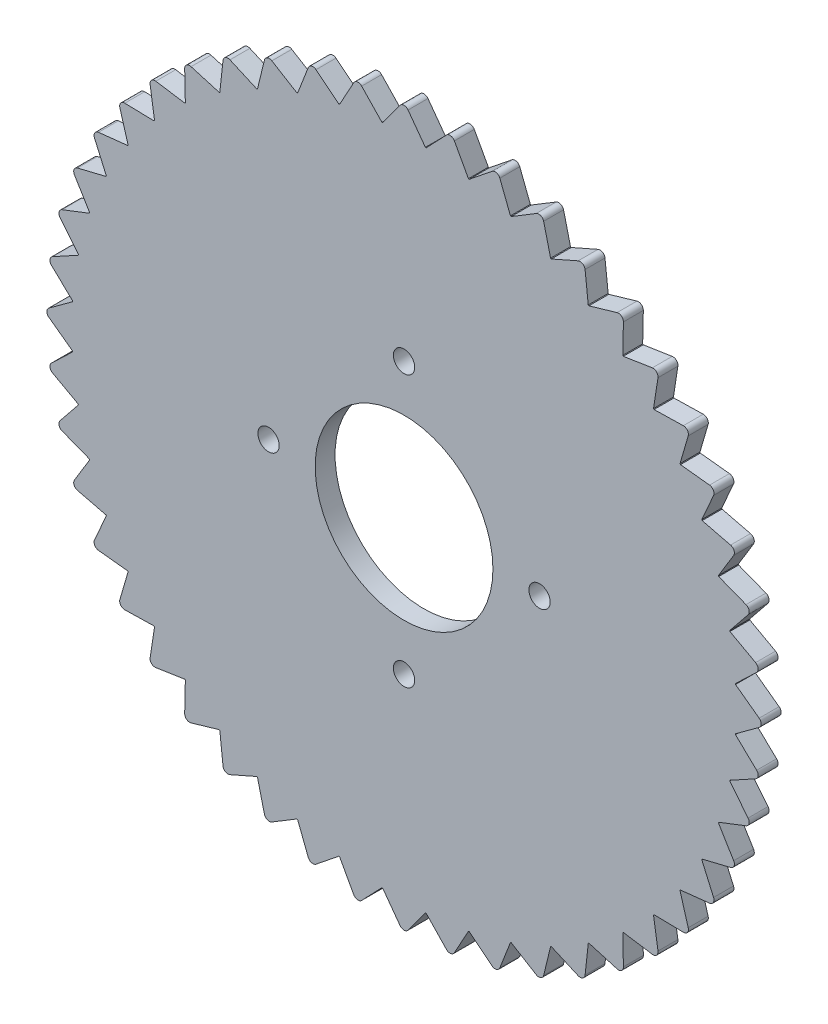
SolidWorks part; units mm, degrees
material "3.0205 (EN-AW 1200)"
ref_plane "Alzado" through (0, 0, 0) normal (0, 0, 1) x (1, 0, 0)
ref_plane "Planta" through (0, 0, 0) normal (0, 1, 0) x (1, 0, 0)
ref_plane "Vista lateral" through (0, 0, 0) normal (1, 0, 0) x (0, 0, -1)
sketch "Croquis1" plane through (0, 0, 0) normal (0, 0, 1) x (1, 0, 0)
  line L0 (0, 46.7) -> (0, -46.7) construction
  circle A0 centre (0, 0) radius 46.7
  circle A1 centre (0, 0) radius 12.5
  circle A2 centre (0, 19.05) radius 1.5
  circle A3 centre (19.05, 0) radius 1.5
  circle A4 centre (0, -19.05) radius 1.5
  circle A5 centre (-19.05, 0) radius 1.5
  point P17 (0, 0)
  dimension "D1" = 93.4
  dimension "D2" = 25
  dimension "D3" = 3
  dimension "D4" = 19.05
  dimension "D5" = 4
extrude "Saliente-Extruir1" add sketch "Croquis1" along normal blind 2.8
sketch "Croquis2" plane through (0, 0, 2.8) normal (0, 0, 1) x (1, 0, 0)
  line L0 (0, 46.7) -> (0, -46.7) construction
  line L1 (0, 50.7) -> (-3, 46.6035)
  line L2 (0, 50.7) -> (3, 46.6035)
  line L3 (6.6177, 50.2663) -> (3.1086, 46.5964)
  line L4 (6.6177, 50.2663) -> (9.0573, 45.8133)
  line L5 (13.1221, 48.9724) -> (9.1641, 45.792)
  line L6 (13.1221, 48.9724) -> (14.9597, 44.2391)
  line L7 (19.4021, 46.8407) -> (15.0628, 44.2041)
  line L8 (19.4021, 46.8407) -> (20.606, 41.908)
  line L9 (25.35, 43.9075) -> (20.7037, 41.8599)
  line L10 (25.35, 43.9075) -> (25.8998, 38.8599)
  line L11 (30.8642, 40.223) -> (25.9904, 38.7994)
  line L12 (30.8642, 40.223) -> (30.7505, 35.1468)
  line L13 (35.8503, 35.8503) -> (30.8324, 35.075)
  line L14 (35.8503, 35.8503) -> (35.075, 30.8324)
  line L15 (40.223, 30.8642) -> (35.1468, 30.7505)
  line L16 (40.223, 30.8642) -> (38.7994, 25.9904)
  line L17 (43.9075, 25.35) -> (38.8599, 25.8998)
  line L18 (43.9075, 25.35) -> (41.8599, 20.7037)
  line L19 (46.8407, 19.4021) -> (41.908, 20.606)
  line L20 (46.8407, 19.4021) -> (44.2041, 15.0628)
  line L21 (48.9724, 13.1221) -> (44.2391, 14.9597)
  line L22 (48.9724, 13.1221) -> (45.792, 9.1641)
  line L23 (50.2663, 6.6177) -> (45.8133, 9.0573)
  line L24 (50.2663, 6.6177) -> (46.5964, 3.1086)
  line L25 (50.7, 0) -> (46.6035, 3)
  line L26 (50.7, 0) -> (46.6035, -3)
  line L27 (50.2663, -6.6177) -> (46.5964, -3.1086)
  line L28 (50.2663, -6.6177) -> (45.8133, -9.0573)
  line L29 (48.9724, -13.1221) -> (45.792, -9.1641)
  line L30 (48.9724, -13.1221) -> (44.2391, -14.9597)
  line L31 (46.8407, -19.4021) -> (44.2041, -15.0628)
  line L32 (46.8407, -19.4021) -> (41.908, -20.606)
  line L33 (43.9075, -25.35) -> (41.8599, -20.7037)
  line L34 (43.9075, -25.35) -> (38.8599, -25.8998)
  line L35 (40.223, -30.8642) -> (38.7994, -25.9904)
  line L36 (40.223, -30.8642) -> (35.1468, -30.7505)
  line L37 (35.8503, -35.8503) -> (35.075, -30.8324)
  line L38 (35.8503, -35.8503) -> (30.8324, -35.075)
  line L39 (30.8642, -40.223) -> (30.7505, -35.1468)
  line L40 (30.8642, -40.223) -> (25.9904, -38.7994)
  line L41 (25.35, -43.9075) -> (25.8998, -38.8599)
  line L42 (25.35, -43.9075) -> (20.7037, -41.8599)
  line L43 (19.4021, -46.8407) -> (20.606, -41.908)
  line L44 (19.4021, -46.8407) -> (15.0628, -44.2041)
  line L45 (13.1221, -48.9724) -> (14.9597, -44.2391)
  line L46 (13.1221, -48.9724) -> (9.1641, -45.792)
  line L47 (6.6177, -50.2663) -> (9.0573, -45.8133)
  line L48 (6.6177, -50.2663) -> (3.1086, -46.5964)
  line L49 (0, -50.7) -> (3, -46.6035)
  line L50 (0, -50.7) -> (-3, -46.6035)
  line L51 (-6.6177, -50.2663) -> (-3.1086, -46.5964)
  line L52 (-6.6177, -50.2663) -> (-9.0573, -45.8133)
  line L53 (-13.1221, -48.9724) -> (-9.1641, -45.792)
  line L54 (-13.1221, -48.9724) -> (-14.9597, -44.2391)
  line L55 (-19.4021, -46.8407) -> (-15.0628, -44.2041)
  line L56 (-19.4021, -46.8407) -> (-20.606, -41.908)
  line L57 (-25.35, -43.9075) -> (-20.7037, -41.8599)
  line L58 (-25.35, -43.9075) -> (-25.8998, -38.8599)
  line L59 (-30.8642, -40.223) -> (-25.9904, -38.7994)
  line L60 (-30.8642, -40.223) -> (-30.7505, -35.1468)
  line L61 (-35.8503, -35.8503) -> (-30.8324, -35.075)
  line L62 (-35.8503, -35.8503) -> (-35.075, -30.8324)
  line L63 (-40.223, -30.8642) -> (-35.1468, -30.7505)
  line L64 (-40.223, -30.8642) -> (-38.7994, -25.9904)
  line L65 (-43.9075, -25.35) -> (-38.8599, -25.8998)
  line L66 (-43.9075, -25.35) -> (-41.8599, -20.7037)
  line L67 (-46.8407, -19.4021) -> (-41.908, -20.606)
  line L68 (-46.8407, -19.4021) -> (-44.2041, -15.0628)
  line L69 (-48.9724, -13.1221) -> (-44.2391, -14.9597)
  line L70 (-48.9724, -13.1221) -> (-45.792, -9.1641)
  line L71 (-50.2663, -6.6177) -> (-45.8133, -9.0573)
  line L72 (-50.2663, -6.6177) -> (-46.5964, -3.1086)
  line L73 (-50.7, 0) -> (-46.6035, -3)
  line L74 (-50.7, 0) -> (-46.6035, 3)
  line L75 (-50.2663, 6.6177) -> (-46.5964, 3.1086)
  line L76 (-50.2663, 6.6177) -> (-45.8133, 9.0573)
  line L77 (-48.9724, 13.1221) -> (-45.792, 9.1641)
  line L78 (-48.9724, 13.1221) -> (-44.2391, 14.9597)
  line L79 (-46.8407, 19.4021) -> (-44.2041, 15.0628)
  line L80 (-46.8407, 19.4021) -> (-41.908, 20.606)
  line L81 (-43.9075, 25.35) -> (-41.8599, 20.7037)
  line L82 (-43.9075, 25.35) -> (-38.8599, 25.8998)
  line L83 (-40.223, 30.8642) -> (-38.7994, 25.9904)
  line L84 (-40.223, 30.8642) -> (-35.1468, 30.7505)
  line L85 (-35.8503, 35.8503) -> (-35.075, 30.8324)
  line L86 (-35.8503, 35.8503) -> (-30.8324, 35.075)
  line L87 (-30.8642, 40.223) -> (-30.7505, 35.1468)
  line L88 (-30.8642, 40.223) -> (-25.9904, 38.7994)
  line L89 (-25.35, 43.9075) -> (-25.8998, 38.8599)
  line L90 (-25.35, 43.9075) -> (-20.7037, 41.8599)
  line L91 (-19.4021, 46.8407) -> (-20.606, 41.908)
  line L92 (-19.4021, 46.8407) -> (-15.0628, 44.2041)
  line L93 (-13.1221, 48.9724) -> (-14.9597, 44.2391)
  line L94 (-13.1221, 48.9724) -> (-9.1641, 45.792)
  line L95 (-6.6177, 50.2663) -> (-9.0573, 45.8133)
  line L96 (-6.6177, 50.2663) -> (-3.1086, 46.5964)
  circle A0 centre (0, 0) radius 46.7 construction
  circle A2 centre (0, 0) radius 46.7
  arc A3 (-3, 46.6035) -> (3, 46.6035) centre (0, 0) ccw
  point P154 (0, 0)
  circle M3 centre (0, 0) radius 46.7
  dimension "D1" = 4
  dimension "D2" = 3
  dimension "D3" = 3
  dimension "D4" = 5.0775
  dimension "D5" = 0
  dimension "D6" = 48
extrude "Saliente-Extruir3" add sketch "Croquis2" against normal blind 2.8 contours L2 L1 M3 | L96 L95 M3 | L94 L93 M3 | L92 L91 M3 | L90 L89 M3 | L88 L87 M3 | L86 L85 M3 | L84 L83 M3 | L82 L81 M3 | L80 L79 M3 | L78 L77 M3 | L76 L75 M3 | L74 L73 M3 | L72 L71 M3 | L70 L69 M3 | L68 L67 M3 | L66 L65 M3 | L64 L63 M3 | L62 L61 M3 | L60 L59 M3 | L58 L57 M3 | L56 L55 M3 | L54 L53 M3 | L52 L51 M3 | L50 L49 A3 M3 | L48 L47 M3 | L46 L45 M3 | L44 L43 M3 | L42 L41 M3 | L40 L39 M3 | L38 L37 M3 | L36 L35 M3 | L34 L33 M3 | L32 L31 M3 | L30 L29 M3 | L28 L27 M3 | L26 L25 M3 | L24 L23 M3 | L22 L21 M3 | L20 L19 M3 | L18 L17 M3 | L16 L15 M3 | L14 L13 M3 | L12 L11 M3 | L10 L9 M3 | L8 L7 M3 | L6 L5 M3 | L4 L3 M3
fillet "Redondeo1" radius 0.7 48 edges at (-6.6177, 50.2663, 1.4) (-13.1221, 48.9724, 1.4) (-19.4021, 46.8407, 1.4) (-25.35, 43.9075, 1.4) (-30.8642, 40.223, 1.4) (-35.8503, 35.8503, 1.4) (-40.223, 30.8642, 1.4) (-43.9075, 25.35, 1.4) (-46.8407, 19.4021, 1.4) (-48.9724, 13.1221, 1.4) (-50.2663, 6.6177, 1.4) (-50.7, 0, 1.4) (-50.2663, -6.6177, 1.4) (-48.9724, -13.1221, 1.4) (-46.8407, -19.4021, 1.4) (-43.9075, -25.35, 1.4) (-40.223, -30.8642, 1.4) (-35.8503, -35.8503, 1.4) (-30.8642, -40.223, 1.4) (-25.35, -43.9075, 1.4) (-19.4021, -46.8407, 1.4) (-13.1221, -48.9724, 1.4) (-6.6177, -50.2663, 1.4) (0, -50.7, 1.4) (6.6177, -50.2663, 1.4) (13.1221, -48.9724, 1.4) (19.4021, -46.8407, 1.4) (25.35, -43.9075, 1.4) (30.8642, -40.223, 1.4) (35.8503, -35.8503, 1.4) (40.223, -30.8642, 1.4) (43.9075, -25.35, 1.4) (46.8407, -19.4021, 1.4) (48.9724, -13.1221, 1.4) (50.2663, -6.6177, 1.4) (50.7, 0, 1.4) (50.2663, 6.6177, 1.4) (48.9724, 13.1221, 1.4) (46.8407, 19.4021, 1.4) (43.9075, 25.35, 1.4) (40.223, 30.8642, 1.4) (35.8503, 35.8503, 1.4) (30.8642, 40.223, 1.4) (25.35, 43.9075, 1.4) (19.4021, 46.8407, 1.4) (13.1221, 48.9724, 1.4) (6.6177, 50.2663, 1.4) (0, 50.7, 1.4)
sketch "Croquis3" plane through (0, 0, 2.8) normal (0, 0, 1) x (1, 0, 0)
  circle A0 centre (0, 0) radius 50.2153
